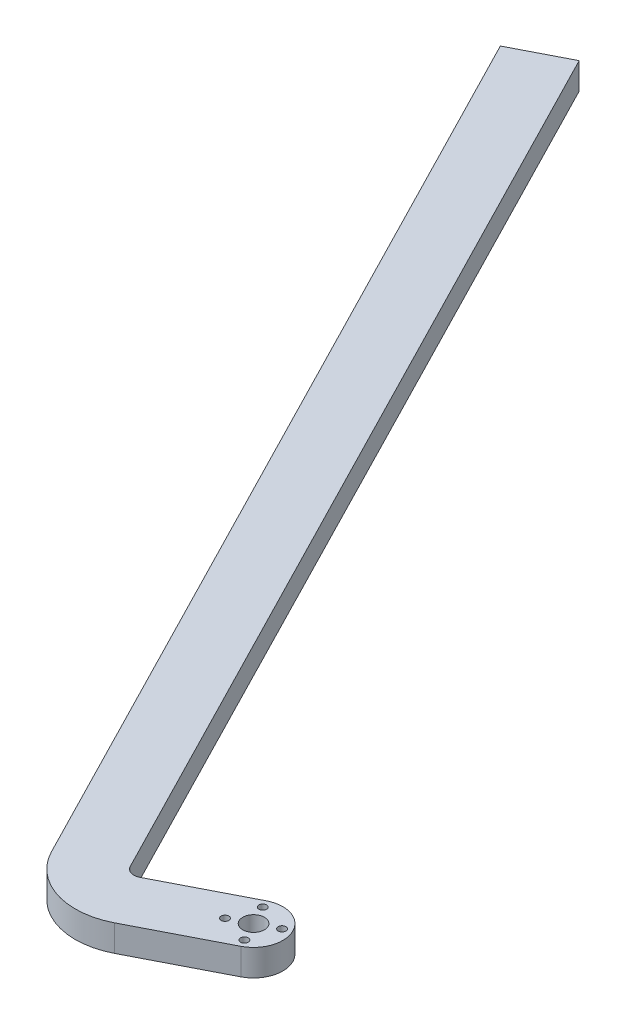
SolidWorks part; units mm, degrees
ref_plane "Front Plane" through (0, 0, 0) normal (0, 0, 1) x (1, 0, 0)
ref_plane "Top Plane" through (0, 0, 0) normal (0, 1, 0) x (1, 0, 0)
ref_plane "Right Plane" through (0, 0, 0) normal (1, 0, 0) x (0, 0, -1)
sketch "Sketch1" plane through (0, 0, 0) normal (0, 1, 0) x (1, 0, 0)
  line L0 (8, 0) -> (-8, 0) construction
  line L1 (0, 11.05) -> (395.35, 11.05)
  line L2 (-11.05, 11.05) -> (-11.05, -11.05) construction
  line L3 (0, -11.05) -> (395.35, -11.05)
  line L4 (395.35, 11.05) -> (395.35, -11.05)
  line L5 (0, 8) -> (0, -8) construction
  circle A0 centre (0, 0) radius 4.1
  circle A1 centre (0, 8) radius 1.455
  circle A2 centre (0, -8) radius 1.455
  circle A3 centre (-8, 0) radius 1.455
  circle A4 centre (8, 0) radius 1.455
  arc A5 (0, 11.05) -> (0, -11.05) centre (0, 0) ccw
  point P4 (-11.05, 0)
  point P5 (0, 0)
  point P17 (0, 0)
  point P18 (0, 0)
  point P21 (0, 0)
  point P22 (0, 0)
  point P23 (0, 0)
  point P24 (0, 0)
  point P25 (-27.653, 0)
  dimension "D3" = 2.91
  dimension "D4" = 8.2
  dimension "D1" = 406.4
  dimension "D2" = 22.1
  dimension "D5" = 16
sketch "Sketch2" plane through (0, 0, 0) normal (0, 1, 0) x (-1, 0, 0)
  line L0 (38.3858, 2.7997) -> (488.5087, -874.1781) construction
  line L1 (38.3858, 2.7997) -> (915.3636, 452.9227) construction
  line L3 (5.0458, -9.8307) -> (36.5651, 6.3471)
  line L4 (38.3858, 2.7997) -> (28.9222, -26.6227) construction
  line L5 (41.9331, 4.6205) -> (220.6412, -343.5579)
  line L6 (-5.0458, 9.8307) -> (26.4735, 26.0085)
  line L7 (61.5945, 14.712) -> (240.3026, -333.4663)
  line L8 (0, 0) -> (185.5746, -361.5564) construction
  line L9 (220.6412, -343.5579) -> (240.3026, -333.4663)
  line L10 (-7.1173, -3.653) -> (7.1173, 3.653) construction
  line L11 (-3.653, 7.1173) -> (3.653, -7.1173) construction
  arc A0 (36.5651, 6.3471) -> (41.9331, 4.6205) centre (38.3858, 2.7997) cw
  circle A1 centre (0, 0) radius 11.05 construction
  arc A2 (26.4735, 26.0085) -> (61.5945, 14.712) centre (38.3858, 2.7997) cw
  arc A3 (-5.0458, 9.8307) -> (5.0458, -9.8307) centre (0, 0) ccw
  circle A4 centre (0, 0) radius 4.1
  circle A5 centre (-3.653, 7.1173) radius 1.455
  circle A6 centre (7.1173, 3.653) radius 1.455
  circle A7 centre (-7.1173, -3.653) radius 1.455
  circle A8 centre (3.653, -7.1173) radius 1.455
  circle A11 centre (8, 0) radius 1.455 construction
  point P5 (0, 0)
  point P20 (0, 0)
  point P27 (0, 0)
  point P29 (0, 0)
  point P35 (0, 0)
  point P36 (0, 0)
  point P38 (0, 0)
  point P39 (0, 0)
  point P41 (0, 0)
  dimension "D1" = 45
  dimension "D2" = 22.1
  dimension "D3" = 406.4
  dimension "D4" = 16
  dimension "D5" = 8.2
extrude "Boss-Extrude2" add sketch "Sketch2" along normal blind 10
